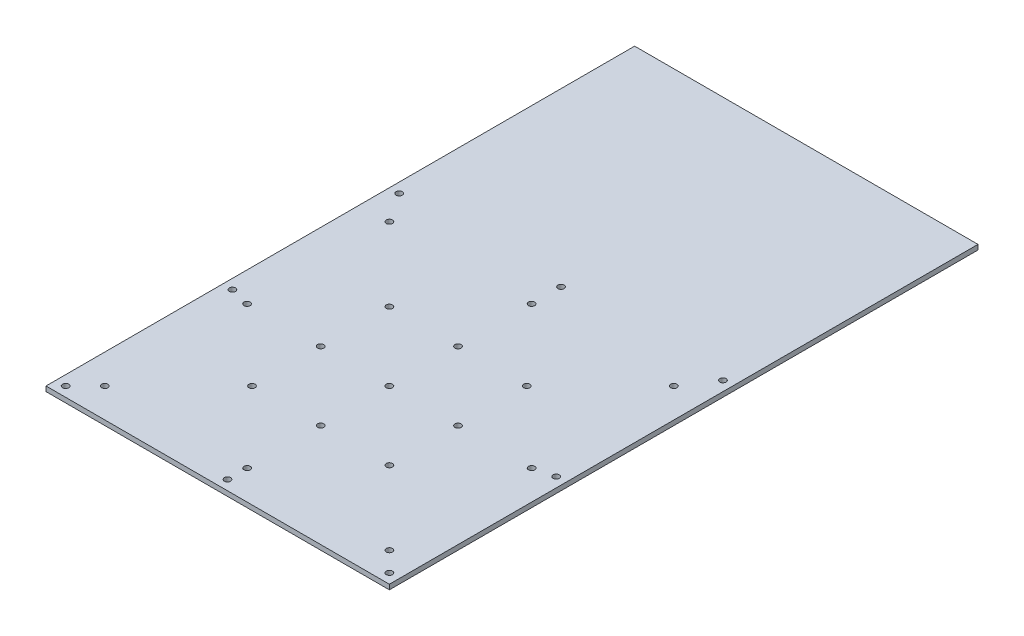
SolidWorks part; units mm, degrees
material "Acrylique (impact moyen-haut)"
ref_plane "Plan de face" through (0, 0, 0) normal (0, 0, 1) x (1, 0, 0)
ref_plane "Plan de dessus" through (0, 0, 0) normal (0, 1, 0) x (1, 0, 0)
ref_plane "Plan de droite" through (0, 0, 0) normal (1, 0, 0) x (0, 0, -1)
sketch "Esquisse1" plane through (0, 0, 0) normal (0, 1, 0) x (1, 0, 0)
  line L0 (0, 0) -> (350, 0)
  line L1 (350, 0) -> (350, 600)
  line L2 (350, 600) -> (0, 600)
  line L3 (0, 600) -> (0, 0)
  line L4 (0, 360) -> (350, 360) construction
  line L5 (340, 0) -> (340, 10) construction
  line L6 (340, 10) -> (10, 10) construction
  line L7 (10, 10) -> (10, 350) construction
  line L8 (10, 350) -> (340, 350) construction
  line L9 (340, 350) -> (340, 10) construction
  line L10 (350, 360) -> (340, 350) construction
  line L11 (0, 360) -> (10, 350) construction
  line L12 (340, 10) -> (350, 0) construction
  line L13 (10, 10) -> (0, 0) construction
  line L14 (40, 360) -> (40, 310) construction
  line L15 (40, 310) -> (0, 310) construction
  line L16 (40, 310) -> (310, 310) construction
  line L17 (310, 310) -> (310, 40) construction
  line L18 (310, 40) -> (40, 40) construction
  line L19 (40, 310) -> (40, 40) construction
  line L20 (175, 310) -> (175, 40) construction
  line L21 (310, 175) -> (40, 175) construction
  line L22 (100, 310) -> (100, 250)
  line L23 (100, 250) -> (40, 250)
  line L24 (40, 250) -> (40, 310)
  line L25 (40, 310) -> (100, 310)
  line L26 (40, 240) -> (100, 240)
  line L27 (100, 240) -> (100, 180)
  line L28 (100, 180) -> (40, 180)
  line L29 (40, 180) -> (40, 240)
  line L30 (110, 250) -> (110, 310)
  line L31 (110, 310) -> (170, 310)
  line L32 (170, 310) -> (170, 250)
  line L33 (170, 250) -> (110, 250)
  line L34 (110, 240) -> (170, 240)
  line L35 (170, 240) -> (170, 180)
  line L36 (170, 180) -> (110, 180)
  line L37 (110, 180) -> (110, 240)
  line L38 (310, 250) -> (310, 310)
  line L39 (310, 310) -> (250, 310)
  line L40 (240, 310) -> (180, 310)
  line L41 (180, 310) -> (180, 250)
  line L42 (180, 240) -> (180, 180)
  line L43 (180, 180) -> (240, 180)
  line L44 (250, 180) -> (310, 180)
  line L45 (310, 180) -> (310, 240)
  line L46 (240, 180) -> (240, 240)
  line L47 (240, 240) -> (180, 240)
  line L48 (180, 250) -> (240, 250)
  line L49 (240, 250) -> (240, 310)
  line L50 (250, 240) -> (250, 180)
  line L51 (310, 240) -> (250, 240)
  line L52 (250, 250) -> (310, 250)
  line L53 (250, 310) -> (250, 250)
  line L54 (40, 40) -> (310, 40) construction
  line L55 (250, 40) -> (250, 100)
  line L56 (240, 100) -> (240, 40)
  line L57 (180, 40) -> (180, 100)
  line L58 (240, 40) -> (180, 40)
  line L59 (310, 40) -> (250, 40)
  line L60 (310, 100) -> (310, 40)
  line L61 (170, 40) -> (170, 100)
  line L62 (110, 40) -> (170, 40)
  line L63 (110, 100) -> (110, 40)
  line L64 (40, 170) -> (40, 110)
  line L65 (100, 170) -> (40, 170)
  line L66 (40, 110) -> (100, 110)
  line L67 (40, 40) -> (100, 40)
  line L68 (40, 100) -> (40, 40)
  line L69 (100, 100) -> (40, 100)
  line L70 (100, 40) -> (100, 100)
  line L71 (250, 100) -> (310, 100)
  line L72 (310, 110) -> (250, 110)
  line L73 (250, 110) -> (250, 170)
  line L74 (180, 100) -> (240, 100)
  line L75 (240, 110) -> (180, 110)
  line L76 (240, 170) -> (240, 110)
  line L77 (310, 170) -> (310, 110)
  line L78 (250, 170) -> (310, 170)
  line L79 (180, 170) -> (240, 170)
  line L80 (180, 110) -> (180, 170)
  line L81 (110, 170) -> (110, 110)
  line L82 (170, 170) -> (110, 170)
  line L83 (170, 110) -> (170, 170)
  line L84 (110, 110) -> (170, 110)
  line L85 (170, 100) -> (110, 100)
  line L86 (100, 110) -> (100, 170)
  line L87 (40, 310) -> (310, 310)
  line L88 (310, 40) -> (40, 40)
  line L89 (40, 40) -> (40, 310)
  line L90 (310, 310) -> (310, 40)
  line L91 (100, 250) -> (110, 240) construction
  line L92 (170, 250) -> (180, 240) construction
  line L93 (240, 250) -> (250, 240) construction
  line L94 (240, 180) -> (250, 170) construction
  line L95 (240, 110) -> (250, 100) construction
  line L96 (170, 110) -> (180, 100) construction
  line L97 (100, 110) -> (110, 100) construction
  line L98 (100, 180) -> (110, 170) construction
  line L99 (175, 40) -> (175, 20) construction
  line L100 (170, 180) -> (180, 170) construction
  line L101 (310, 175) -> (330, 175) construction
  line L102 (175, 310) -> (175, 330) construction
  line L103 (310, 310) -> (330, 330) construction
  line L104 (40, 310) -> (20, 330) construction
  line L105 (40, 40) -> (20, 20) construction
  line L107 (310, 40) -> (330, 20) construction
  line L108 (40, 175) -> (20, 175) construction
  line L109 (20, 330) -> (330, 330) construction
  line L110 (330, 330) -> (330, 20) construction
  line L111 (330, 20) -> (20, 20) construction
  line L112 (20, 20) -> (20, 330) construction
  circle A0 centre (10, 10) radius 3.175
  circle A1 centre (175, 10) radius 3.175
  circle A2 centre (340, 10) radius 3.175
  circle A3 centre (340, 350) radius 3.175
  circle A4 centre (340, 180) radius 3.175
  circle A5 centre (10, 180) radius 3.175
  circle A6 centre (10, 350) radius 3.175
  circle A7 centre (175, 350) radius 3.175
  circle A8 centre (320, 320) radius 3.175
  circle A9 centre (175, 320) radius 3.175
  circle A10 centre (30, 320) radius 3.175
  circle A11 centre (105, 245) radius 3.175
  circle A12 centre (175, 245) radius 3.175
  circle A13 centre (245, 245) radius 3.175
  circle A14 centre (175, 175) radius 3.175
  circle A15 centre (245, 175) radius 3.175
  circle A16 centre (320, 175) radius 3.175
  circle A17 centre (105, 175) radius 3.175
  circle A18 centre (30, 175) radius 3.175
  circle A19 centre (105, 105) radius 3.175
  circle A20 centre (175, 105) radius 3.175
  circle A21 centre (245, 105) radius 3.175
  circle A22 centre (320, 30) radius 3.175
  circle A23 centre (175, 30) radius 3.175
  circle A24 centre (30, 30) radius 3.175
  dimension "D8" = 50
  dimension "D1" = 350
  dimension "D2" = 600
  dimension "D3" = 360
  dimension "D4" = 10
  dimension "D5" = 10
  dimension "D6" = 10
  dimension "D7" = 10
  dimension "D9" = 40
  dimension "D10" = 270
  dimension "D11" = 270
  dimension "D12" = 40
  dimension "D13" = 60
  dimension "D14" = 60
  dimension "D15" = 10
  dimension "D16" = 60
  dimension "D17" = 10
  dimension "D18" = 60
  dimension "D19" = 20
  dimension "D21" = 20
  dimension "D22" = 20
  dimension "D23" = 20
extrude "Boss.-Extru.1" add sketch "Esquisse1" along normal blind 5 contours L2 L3 L0 L1 A7 A6 A5 A4 A3 A2 A1 A0 L38 L90 L45 L77 L60 L59 L88 L58 L62 L67 L68 L89 L64 L29 L24 L25 L87 L31 L40 L39 | L90 L52 L53 L87 L49 L48 L41 L32 L33 L30 L22 L23 L89 L26 L27 L28 L65 L86 L66 L69 L70 L88 L63 L85 L61 L57 L74 L56 L55 L71 L72 L73 L78 L44 L50 L51 L84 L81 L82 L83 L47 | L33 L32 L31 L30 | L25 L24 L23 L22 | L29 L28 L27 L26 | L37 L36 L35 L34 | L46 L47 L42 L43 | L48 L49 L40 L41 | L39 L53 L52 L38 | L45 L51 L50 L44 | L78 L73 L72 L77 | L71 L55 L59 L60 | L74 L57 L58 L56 | L80 L75 L76 L79 | L81 L84 L83 L82 | L61 L85 L63 L62 | L67 L70 L69 L68 | L66 L86 L65 L64
